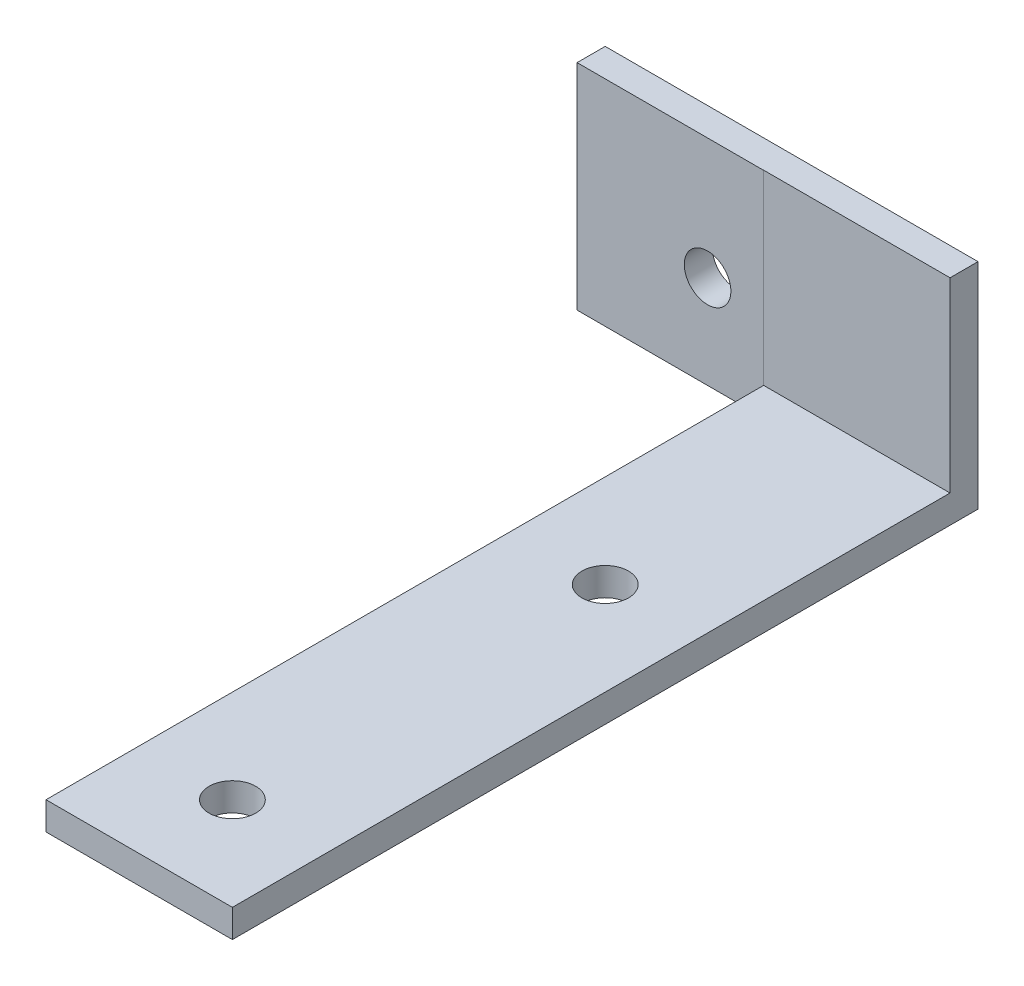
SolidWorks part; units mm, degrees
material "ABS"
ref_plane "Front Plane" through (0, 0, 0) normal (0, 0, 1) x (1, 0, 0)
ref_plane "Top Plane" through (0, 0, 0) normal (0, 1, 0) x (1, 0, 0)
ref_plane "Right Plane" through (0, 0, 0) normal (1, 0, 0) x (0, 0, -1)
sketch "Sketch1" plane through (0, 0, 0) normal (0, 1, 0) x (1, 0, 0)
  line L0 (0, 40) -> (0, -40) construction
  line L1 (-10, 40) -> (10, 40)
  line L2 (-10, 40) -> (-10, -40)
  line L3 (-10, -40) -> (10, -40)
  line L4 (10, 40) -> (10, -40)
  line L5 (-10, 40) -> (10, -40) construction
  line L6 (-10, -40) -> (10, 40) construction
  circle A1 centre (0, -30) radius 2.5
  circle A2 centre (0, 10) radius 2.5
  point P0 (0, 0)
extrude "Boss-Extrude1" add sketch "Sketch1" along normal blind 3
sketch "Sketch2" plane through (0, 3, 0) normal (0, 1, 0) x (1, 0, 0)
  line L0 (10, -40) -> (10, 40) construction
  line L1 (-10, 40) -> (10, 40)
  line L2 (-10, 40) -> (-10, 37)
  line L3 (-10, 37) -> (10, 37)
  line L4 (10, 40) -> (10, 37)
extrude "Boss-Extrude2" add sketch "Sketch2" along normal blind 20
sketch "Sketch4" plane through (-10, 0, 0) normal (-1, 0, 0) x (0, 0, 1)
  line L0 (-40, 0) -> (40, 0) construction
  line L1 (-40, 23) -> (-36.9847, 23)
  line L2 (-40, 23) -> (-40, 0)
  line L3 (-40, 0) -> (-36.9847, 0)
  line L4 (-36.9847, 23) -> (-36.9847, 0)
extrude "Boss-Extrude4" add sketch "Sketch4" along normal blind 20
sketch "Sketch7" plane through (0, 0, -40) normal (0, 0, -1) x (-1, 0, 0)
  line L0 (0, 0) -> (0, 23) construction
  line L1 (-10, 23) -> (30, 23) construction
  circle A0 centre (16, 10) radius 2.5
extrude "Cut-Extrude2" cut sketch "Sketch7" against normal blind 20
